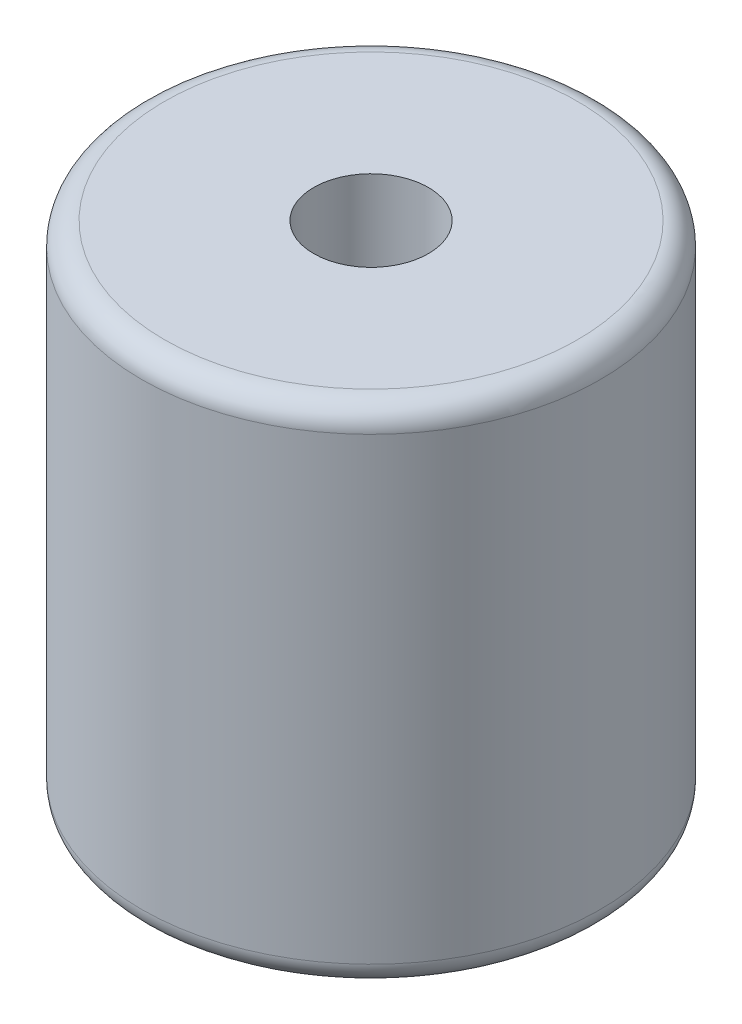
SolidWorks part; units mm, degrees
ref_plane "Front Plane" through (0, 0, 0) normal (0, 0, 1) x (1, 0, 0)
ref_plane "Top Plane" through (0, 0, 0) normal (0, 1, 0) x (1, 0, 0)
ref_plane "Right Plane" through (0, 0, 0) normal (1, 0, 0) x (0, 0, -1)
ref_plane "Plane1" through (0, 0, 0) normal (0, 0, -1) x (-1, 0, 0)
sketch "Sketch1" plane through (0, 0, 0) normal (0, 0, -1) x (-1, 0, 0)
  line L0 (-6, -21) -> (-6, -5)
  line L1 (-6, -5) -> (-2.5, -5)
  line L2 (-2.5, -5) -> (-2.5, 0)
  line L3 (-2.5, 0) -> (-9, 0)
  line L4 (-10, -1) -> (-10, -21)
  line L5 (-9, -22) -> (-7, -22)
  line L6 (0, -22) -> (0, 0) construction
  arc A0 (-9, 0) -> (-10, -1) centre (-9, -1) ccw
  arc A1 (-10, -21) -> (-9, -22) centre (-9, -21) ccw
  arc A2 (-7, -22) -> (-6, -21) centre (-7, -21) ccw
revolve "Revolve1" add sketch "Sketch1" angle 360 about L6
